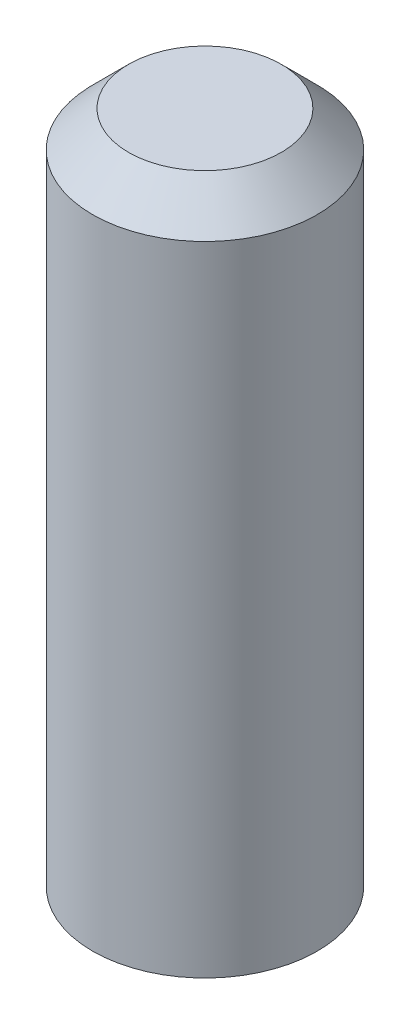
SolidWorks part; units mm, degrees
material "Chrome Stainless Steel"
ref_plane "Front" through (0, 0, 0) normal (0, 0, 1) x (1, 0, 0)
ref_plane "Top" through (0, 0, 0) normal (0, 1, 0) x (1, 0, 0)
ref_plane "Right" through (0, 0, 0) normal (1, 0, 0) x (0, 0, -1)
sketch "Sketch1" plane through (0, 0, 0) normal (0, 1, 0) x (1, 0, 0)
  circle A0 centre (0, 0) radius 2.5
  dimension "D1" = 5
extrude "Boss-Extrude1" add sketch "Sketch1" along normal blind 15 contours A0
chamfer "Chamfer1" distance 0.8 angle 45 1 edges at (0, 15, 2.5)
